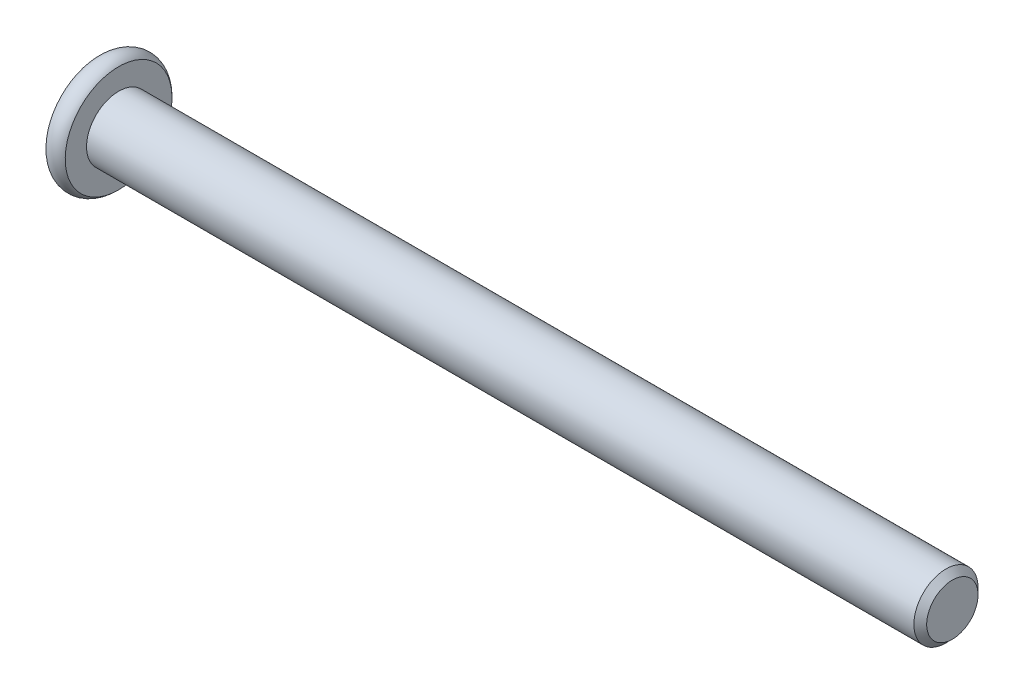
SolidWorks part; units mm, degrees
material "Plain Carbon Steel"
ref_plane "Front Plane" through (0, 0, 0) normal (0, 0, 1) x (1, 0, 0)
ref_plane "Top Plane" through (0, 0, 0) normal (0, 1, 0) x (1, 0, 0)
ref_plane "Right Plane" through (0, 0, 0) normal (1, 0, 0) x (0, 0, -1)
other "M5 x 15"
sketch "Sketch2" plane through (0, 0, 0) normal (1, 0, 0) x (0, 0, -1)
  circle A0 centre (0, 0) radius 2.5
  dimension "D1" = 5
extrude "Boss-Extrude1" add sketch "Sketch2" against normal blind 65
chamfer "Chamfer1" distance 0.5 angle 45 1 edges at (0, 0, -2.5)
sketch "Sketch6" plane through (0, 0, 0) normal (0, 0, 1) x (1, 0, 0)
  line L0 (-66.5, 0) -> (-66.5, 4.1614)
  line L1 (-66.5, 0) -> (-65, 0)
  line L2 (-65.75, 0) -> (-65.75, 3.5) construction
  line L6 (-65, 4.1614) -> (-65, 0)
  line L8 (-65, 0) -> (-14.6471, 0) construction
  line L10 (-65, 2.5) -> (-65, -2.5) construction
  arc A0 (-66.5, 4.1614) -> (-65, 4.1614) centre (-65.75, 3.5) cw
  dimension "D3" = 1
  dimension "D1" = 1.5
  dimension "D2" = 9
revolve "Revolve1" add sketch "Sketch6" angle 360 about L8
sketch "Sketch7" plane through (-66.5, 0, 0) normal (-1, 0, 0) x (0, 0, 1)
  line L1 (0, 1.7321) -> (-1.5, 0.866)
  line L2 (-1.5, 0.866) -> (-1.5, -0.866)
  line L3 (-1.5, -0.866) -> (0, -1.7321)
  line L4 (0, -1.7321) -> (1.5, -0.866)
  line L5 (1.5, -0.866) -> (1.5, 0.866)
  line L6 (1.5, 0.866) -> (0, 1.7321)
  circle A0 centre (0, 0) radius 1.5 construction
  dimension "D1" = 3
extrude "Cut-Extrude1" cut sketch "Sketch7" against normal blind 2.3
sketch "Sketch8" plane through (-66.5, 0, 0) normal (-1, 0, 0) x (0, 0, 1)
  circle A0 centre (0, 0) radius 1.7821
  dimension "D1" = 0.05
extrude "Cut-Extrude2" cut sketch "Sketch8" against normal blind 1 draft 45
